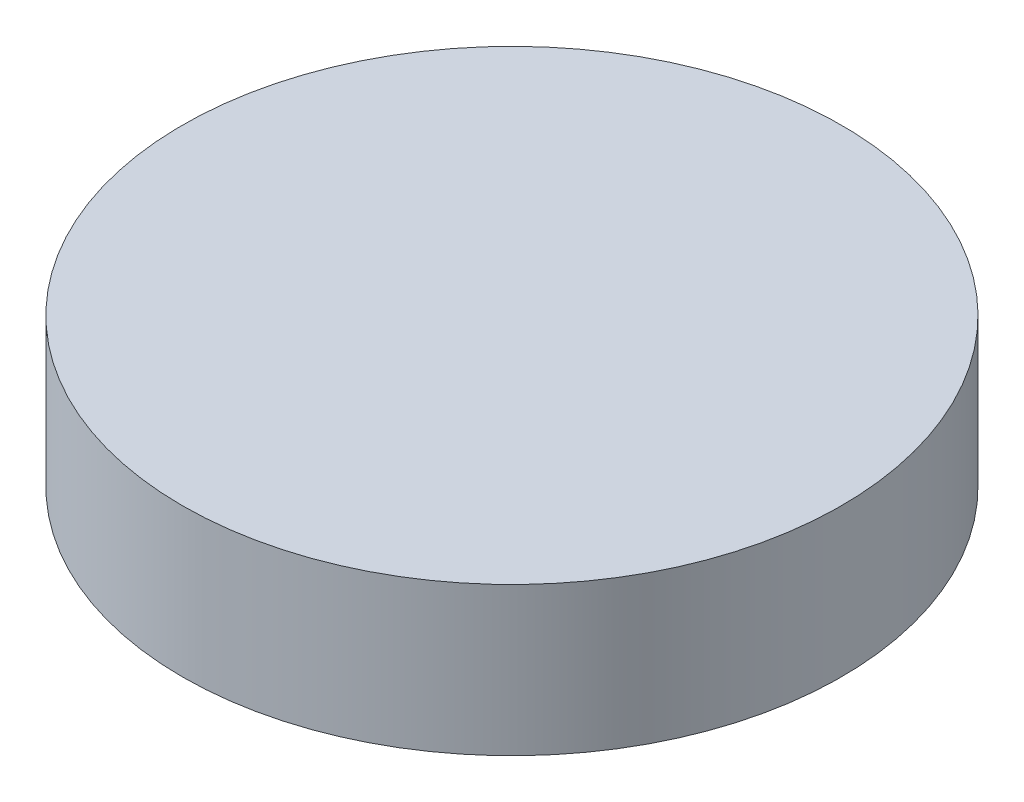
SolidWorks part; units mm, degrees
material "Alloy Steel"
ref_plane "Front Plane" through (0, 0, 0) normal (0, 0, 1) x (1, 0, 0)
ref_plane "Top Plane" through (0, 0, 0) normal (0, 1, 0) x (1, 0, 0)
ref_plane "Right Plane" through (0, 0, 0) normal (1, 0, 0) x (0, 0, -1)
sketch "Sketch1" plane through (0, 0, 0) normal (0, 1, 0) x (1, 0, 0)
  circle A0 centre (0, 0) radius 12.25
  dimension "D1" = 24.5
extrude "Boss-Extrude1" add sketch "Sketch1" along normal blind 5.5118
